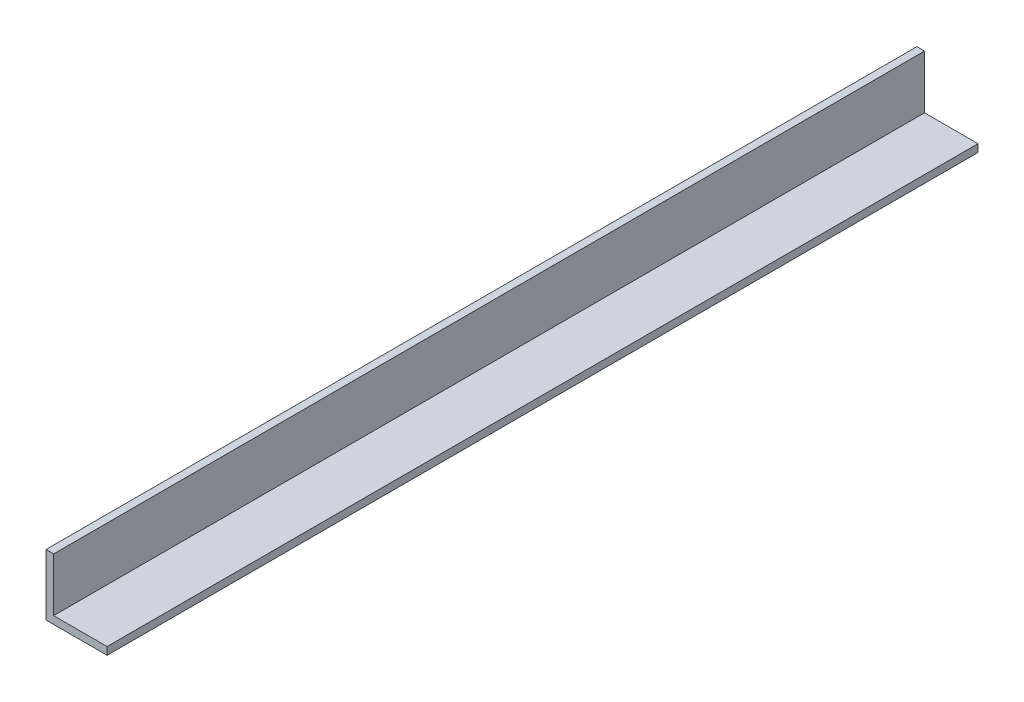
SolidWorks part; units mm, degrees
ref_plane "Front Plane" through (0, 0, 0) normal (0, 0, 1) x (1, 0, 0)
ref_plane "Top Plane" through (0, 0, 0) normal (0, 1, 0) x (1, 0, 0)
ref_plane "Right Plane" through (0, 0, 0) normal (1, 0, 0) x (0, 0, -1)
sketch "Sketch1" plane through (0, 0, 0) normal (0, 0, 1) x (1, 0, 0)
  line L0 (0, 25.4) -> (0, 0)
  line L1 (0, 0) -> (25.4, 0)
  line L2 (25.4, 0) -> (25.4, 3.175)
  line L3 (25.4, 3.175) -> (3.175, 3.175)
  line L4 (3.175, 3.175) -> (3.175, 25.4)
  line L5 (3.175, 25.4) -> (0, 25.4)
  dimension "D1" = 25.4
  dimension "D2" = 3.175
extrude "Boss-Extrude1" add sketch "Sketch1" along normal mid plane 361.95
